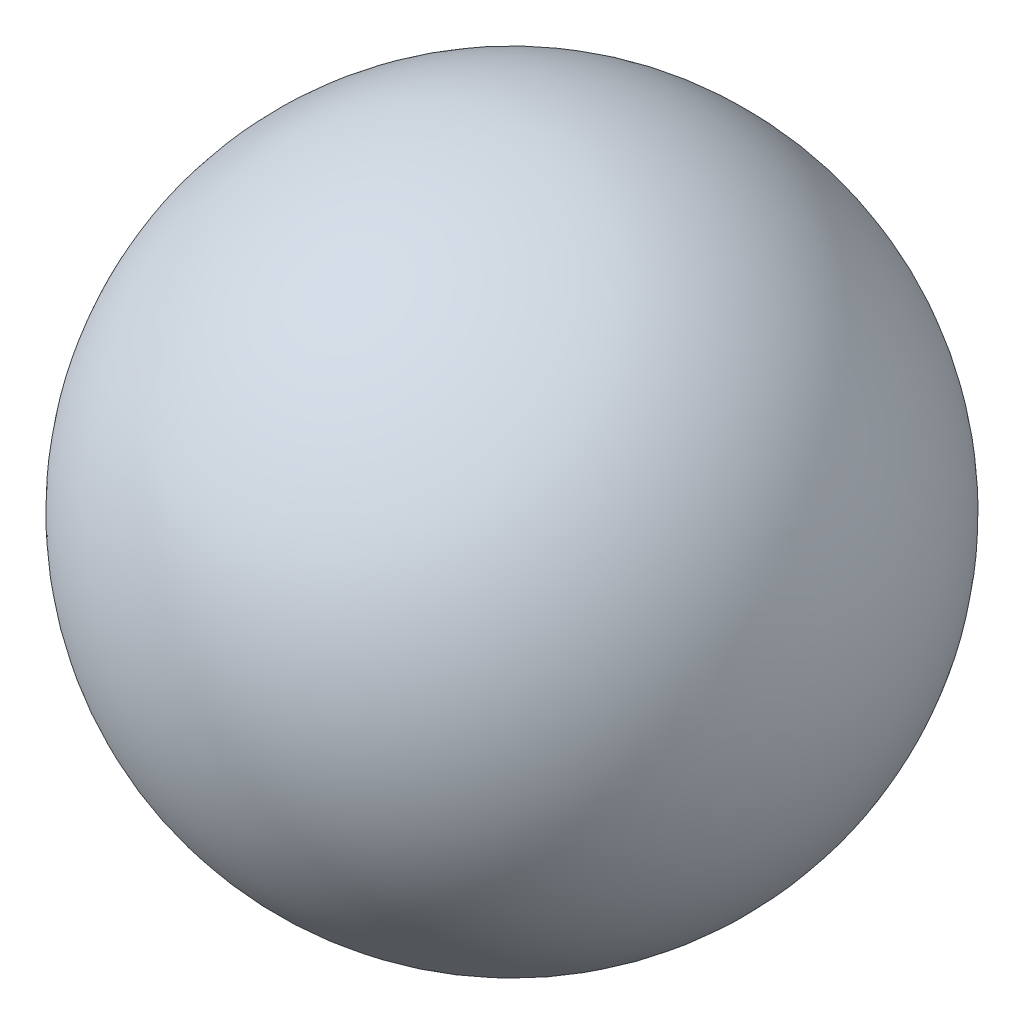
SolidWorks part; units mm, degrees
ref_plane "Front Plane" through (0, 0, 0) normal (0, 0, 1) x (1, 0, 0)
ref_plane "Top Plane" through (0, 0, 0) normal (0, 1, 0) x (1, 0, 0)
ref_plane "Right Plane" through (0, 0, 0) normal (1, 0, 0) x (0, 0, -1)
ref_plane "Plane1" through (0, 0, 0) normal (0, 0, 1) x (1, 0, 0)
sketch "Sketch1" plane through (0, 0, 0) normal (0, 0, 1) x (1, 0, 0)
  line L0 (3.3375, 7.325) -> (0.1625, 7.325)
  line L1 (3.3375, 7.325) -> (0.1625, 7.325) construction
  arc A0 (0.1625, 7.325) -> (3.3375, 7.325) centre (1.75, 7.325) cw
revolve "Revolve1" add sketch "Sketch1" angle 360 about L1
